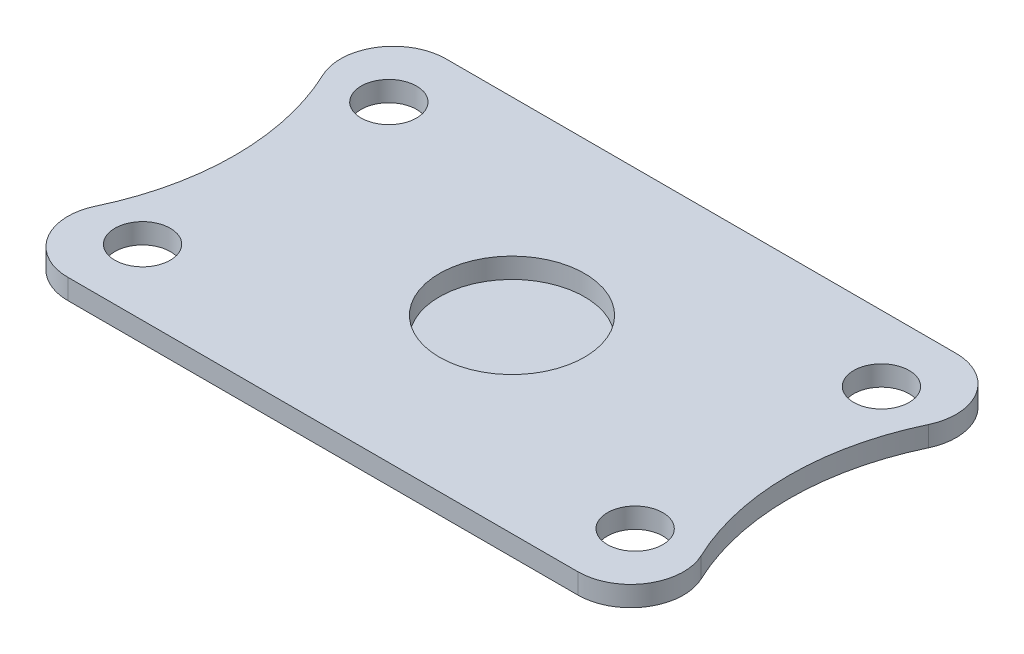
SolidWorks part; units mm, degrees
ref_plane "正面" through (0, 0, 0) normal (0, 0, 1) x (1, 0, 0)
ref_plane "平面" through (0, 0, 0) normal (0, 1, 0) x (1, 0, 0)
ref_plane "右側面" through (0, 0, 0) normal (1, 0, 0) x (0, 0, -1)
sketch "ｽｹｯﾁ2" plane through (0, 0, 0) normal (0, 1, 0) x (1, 0, 0)
  line B0 (-29, 21.5) -> (29, 21.5)
  line B1 (-29, -21.5) -> (29, -21.5)
  line B2 (-28, 14) -> (28, 14)
  line B3 (28, 14) -> (28, -14)
  line B4 (-28, 14) -> (-28, -14)
  line B5 (-28, -14) -> (28, -14)
  circle B6 centre (28, 14) radius 3.15
  arc B7 (34.4178, 12.9218) -> (29, 21.5) centre (29, 15.5) ccw
  circle B8 centre (28, -14) radius 3.15
  arc B9 (29, -21.5) -> (34.4178, -12.9218) centre (29, -15.5) ccw
  arc B10 (34.4178, 12.9218) -> (34.4178, -12.9218) centre (61.5714, 0) ccw
  circle B11 centre (-28, 14) radius 3.15
  arc B12 (-29, 21.5) -> (-34.4178, 12.9218) centre (-29, 15.5) ccw
  circle B13 centre (-28, -14) radius 3.15
  arc B14 (-34.4178, -12.9218) -> (-29, -21.5) centre (-29, -15.5) ccw
  arc B15 (-34.4178, -12.9218) -> (-34.4178, 12.9218) centre (-61.5714, 0) ccw
  circle B16 centre (0, 0) radius 8.25
sketch_block_instance "BLKF015-1"
sketch_block "BLKF015"
extrude "ﾎﾞｽ - 押し出し1" add sketch "ｽｹｯﾁ2" along normal blind 2.3 contours B15 B14 B1 B9 B10 B7 B0 B12 B13 B4 B11 B2 B6 B3 B8 B5 | B13 B5 B8 B3 B6 B2 B11 B4 B16
sketch "ｽｹｯﾁ4" plane through (0, 0, 0) normal (0, 0, 1) x (1, 0, 0)
  line L0 (0, 0) -> (0, -4) construction
  line L1 (0, -4) -> (16, -4)
  line L2 (0, 0) -> (16, 0)
  line L3 (16, 0) -> (16, -4)
  line L4 (16, 0) -> (13, 0)
  line L5 (13, 0) -> (13, -3)
  arc A0 (16, -3) -> (13, 0) centre (13, -3) ccw
  dimension "D1" = 4
  dimension "D2" = 16
  dimension "D3" = 3
revolve "回転1" add sketch "ｽｹｯﾁ4" angle 360 about L0
